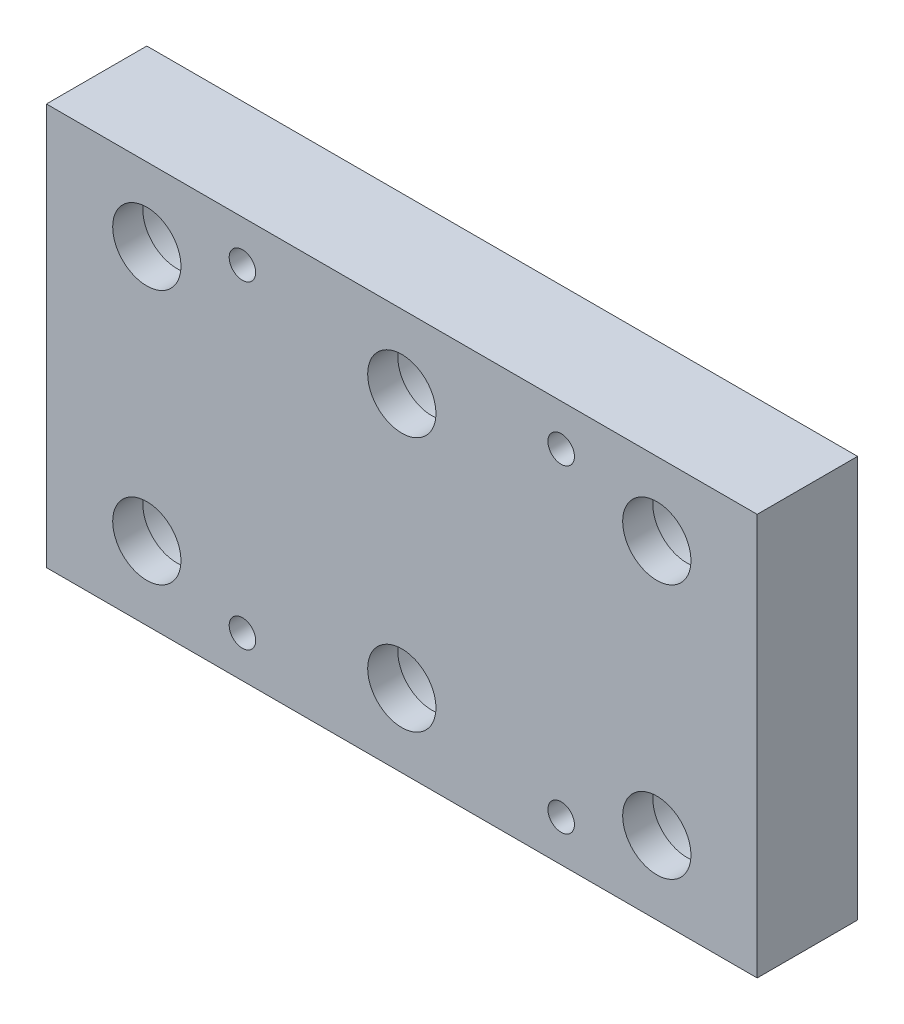
SolidWorks part; units mm, degrees
ref_plane "Front Plane" through (0, 0, 0) normal (0, 0, 1) x (1, 0, 0)
ref_plane "Top Plane" through (0, 0, 0) normal (0, 1, 0) x (1, 0, 0)
ref_plane "Right Plane" through (0, 0, 0) normal (1, 0, 0) x (0, 0, -1)
sketch "Sketch1" plane through (0, 0, 0) normal (0, 0, 1) x (1, 0, 0)
  line L0 (0, 20) -> (0, -20) construction
  line L1 (35.4, 20) -> (-35.4, 20)
  line L2 (35.4, 20) -> (35.4, -20)
  line L3 (35.4, -20) -> (-35.4, -20)
  line L4 (-35.4, 20) -> (-35.4, -20)
  line L5 (-35.4, 0) -> (35.4, 0) construction
  dimension "D1" = 70.8
  dimension "D2" = 40
extrude "Boss-Extrude1" add sketch "Sketch1" along normal blind 10
sketch "Sketch2" plane through (0, 0, 10) normal (0, 0, 1) x (1, 0, 0)
  line L0 (-15.875, -15.875) -> (15.875, -15.875) construction
  line L1 (15.875, -15.875) -> (15.875, 15.875) construction
  line L2 (15.875, 15.875) -> (-15.875, 15.875) construction
  line L4 (0, 0) -> (-35.4, 0) construction
  line L5 (-15.875, 15.875) -> (-15.875, -15.875) construction
  line L6 (0, 20) -> (0, -20) construction
  line L7 (35.4, 20) -> (-35.4, 20) construction
  line L8 (35.4, -20) -> (-35.4, -20) construction
  line L9 (-35.4, 20) -> (-35.4, -20) construction
  line L10 (35.4, 20) -> (35.4, -20) construction
  line L11 (-35.4, 0) -> (35.4, 0) construction
  line L12 (0, 15.875) -> (0, -15.875) construction
  line L13 (15.875, 0) -> (-25.4006, 0) construction
  line L17 (0, 10.95) -> (0, -20.8) construction
  circle A0 centre (15.875, -15.875) radius 1.32
  circle A1 centre (-15.875, -15.875) radius 1.32
  circle A2 centre (-15.875, 15.875) radius 1.32
  circle A3 centre (15.875, 15.875) radius 1.32
  dimension "D1" = 2.64
  dimension "D4" = 31.75
  dimension "D5" = 31.75
  dimension "D2" = 2
  dimension "D3" = 2
extrude "Cut-Extrude1" cut sketch "Sketch2" against normal through all
sketch "Sketch3" plane through (0, 0, 0) normal (0, 0, -1) x (-1, 0, 0)
  line L0 (-25.4, -12.7) -> (25.4, -12.7) construction
  line L1 (25.4, -12.7) -> (25.4, 12.7) construction
  line L2 (25.4, 12.7) -> (-25.4, 12.7) construction
  line L3 (-25.4, 12.7) -> (-25.4, -12.7) construction
  line L4 (-35.4, 20) -> (35.4, 20) construction
  line L5 (35.4, 20) -> (35.4, -20) construction
  line L6 (35.4, -20) -> (-35.4, -20) construction
  line L7 (-35.4, -20) -> (-35.4, 20) construction
  line L8 (0, -20) -> (0, 20) construction
  line L10 (-35.4, 0) -> (35.4, 0) construction
  line L11 (-25.4, 0) -> (37.1361, 0) construction
  circle A0 centre (-25.4, -12.7) radius 3.4
  circle A1 centre (0, -12.7) radius 3.4
  circle A2 centre (25.4, -12.7) radius 3.4
  circle A4 centre (0, 12.7) radius 3.4
  circle A5 centre (25.4, 12.7) radius 3.4
  circle A7 centre (-25.4, 12.7) radius 3.4
  dimension "D1" = 6.8
  dimension "D4" = 25.4
  dimension "D5" = 50.8
  dimension "D2" = 3
  dimension "D3" = 2
extrude "Cut-Extrude2" cut sketch "Sketch3" against normal through all
sketch "Sketch4" plane through (0, 0, 0) normal (0, 0, -1) x (-1, 0, 0)
  line L0 (-35.4, 0) -> (35.4, 0) construction
  line L2 (-35.4, 30) -> (-35.4, -20) construction
  circle A0 centre (25.4, -12.7) radius 5.375
  circle A1 centre (0, -12.7) radius 5.375
  circle A2 centre (-25.4, -12.7) radius 5.375
  circle A3 centre (0, 12.7) radius 5.375
  circle A4 centre (-25.4, 12.7) radius 5.375
  circle A5 centre (25.4, 12.7) radius 5.375
  circle A6 centre (0, 12.7) radius 3.4 construction
  circle A7 centre (-25.4, 12.7) radius 3.4 construction
  dimension "D1" = 10.75
  dimension "D4" = 10
  dimension "D5" = 10
  dimension "D2" = 3
  dimension "D3" = 2
extrude "Cut-Extrude3" cut sketch "Sketch4" against normal blind 7
equation "\"hole_screw_1_4_20\"= 6"
equation "\"inch\"=25.43"
equation "\"AA\"= 23.35"
